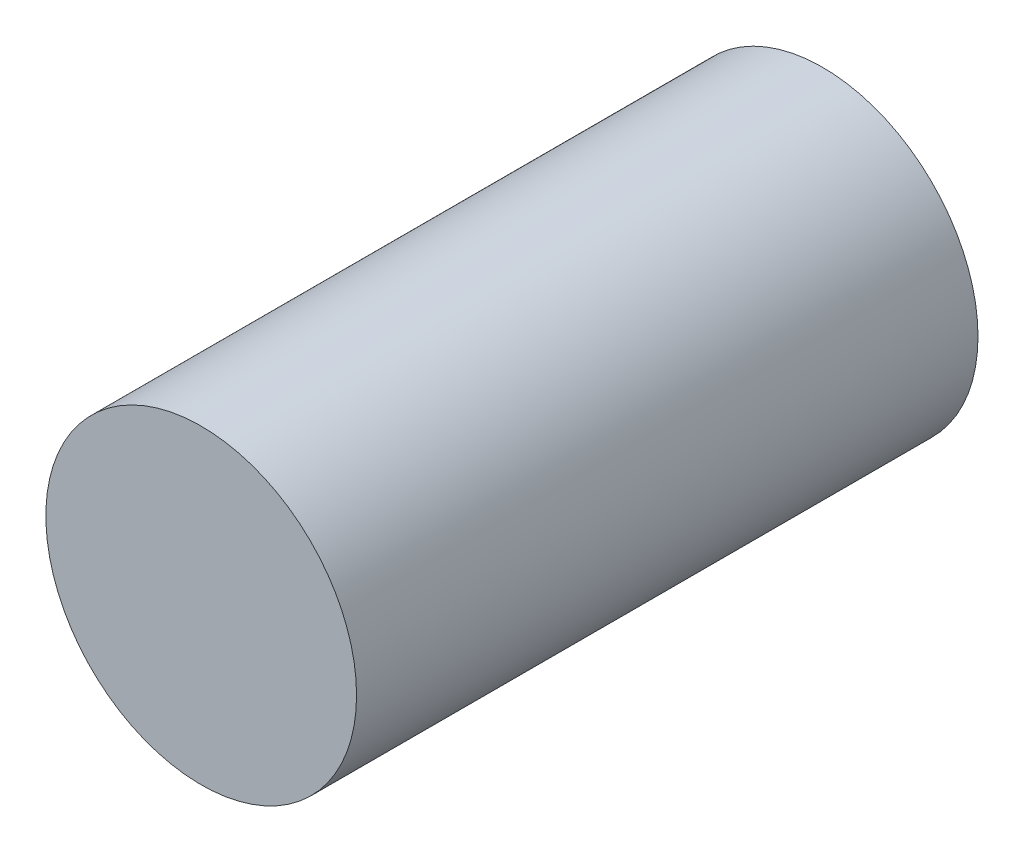
SolidWorks part; units mm, degrees
material "Alloy Steel"
ref_plane "Front" through (0, 0, 0) normal (0, 0, 1) x (1, 0, 0)
ref_plane "Top" through (0, 0, 0) normal (0, 1, 0) x (1, 0, 0)
ref_plane "Right" through (0, 0, 0) normal (1, 0, 0) x (0, 0, -1)
sketch "Sketch1" plane through (0, 0, 0) normal (0, 0, 1) x (1, 0, 0)
  circle A0 centre (0, 0) radius 3.175
  dimension "D1" = 6.35
extrude "Boss-Extrude1" add sketch "Sketch1" along normal blind 12.7
